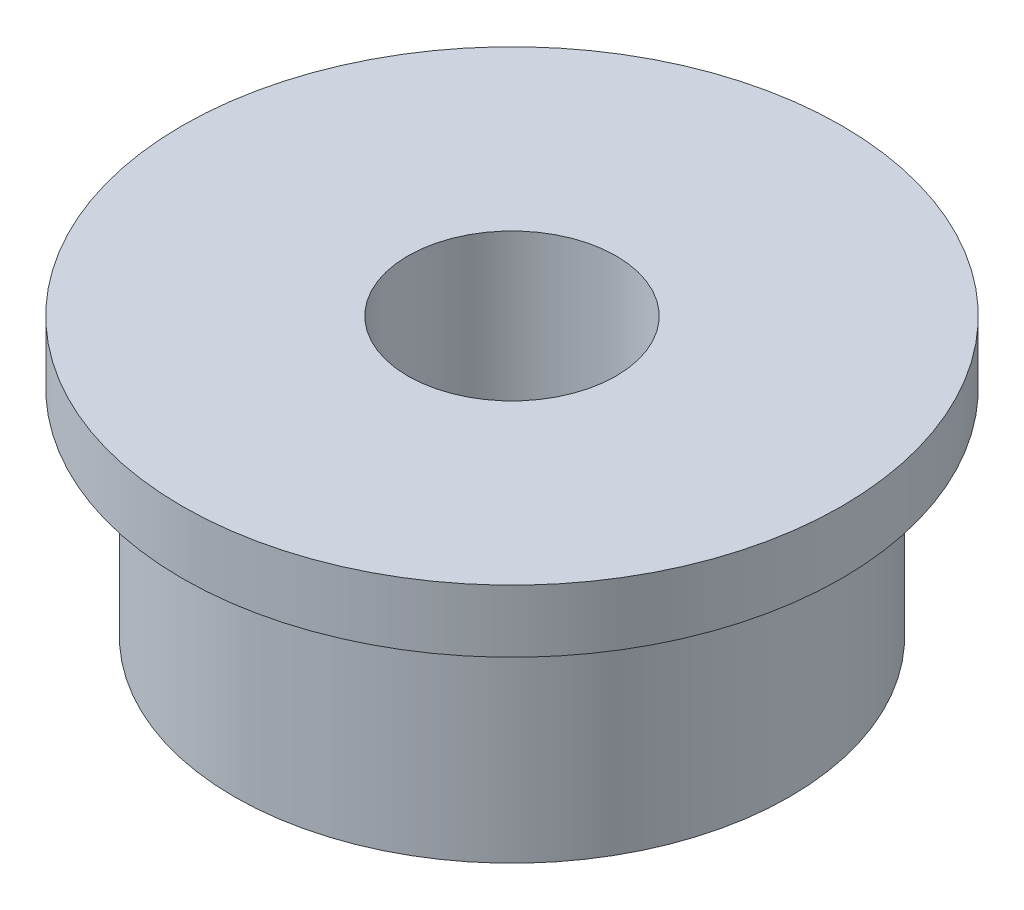
SolidWorks part; units mm, degrees
ref_plane "前视基准面" through (0, 0, 0) normal (0, 0, 1) x (1, 0, 0)
ref_plane "上视基准面" through (0, 0, 0) normal (0, 1, 0) x (1, 0, 0)
ref_plane "右视基准面" through (0, 0, 0) normal (1, 0, 0) x (0, 0, -1)
other "Configuration Table"
sketch "草图1" plane through (0, 0, 0) normal (0, 0, 1) x (1, 0, 0)
  line L0 (0, 0) -> (0, 3.4761) construction
  line L1 (1.5, 4) -> (4.75, 4)
  line L2 (4.75, 4) -> (4.75, 3.1)
  line L3 (4.75, 3.1) -> (4, 3.1)
  line L4 (4, 3.1) -> (4, 0)
  line L5 (4, 0) -> (1.5, 0)
  line L6 (1.5, 4) -> (1.5, 0)
  dimension "D1" = 4.75
  dimension "D2" = 4
  dimension "D3" = 4
  dimension "D4" = 0.9
  dimension "D5" = 1.5
revolve "旋转1" add sketch "草图1" angle 360 about L0
